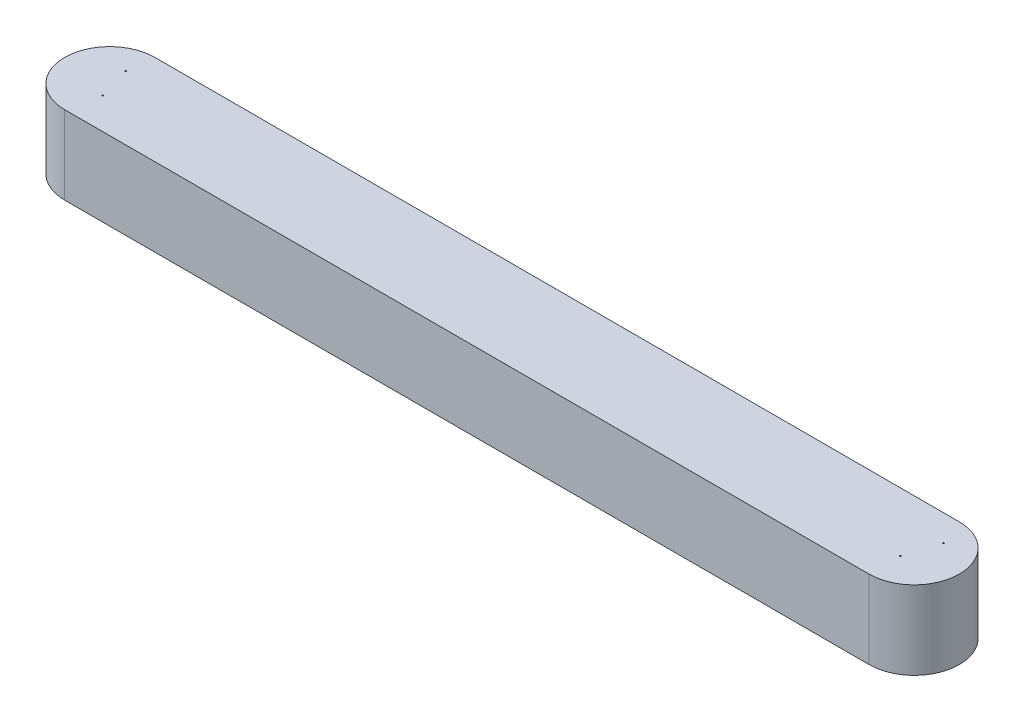
SolidWorks part; units mm, degrees
ref_plane "Front Plane" through (0, 0, 0) normal (0, 0, 1) x (1, 0, 0)
ref_plane "Top Plane" through (0, 0, 0) normal (0, 1, 0) x (1, 0, 0)
ref_plane "Right Plane" through (0, 0, 0) normal (1, 0, 0) x (0, 0, -1)
sketch "Sketch1" plane through (0, 0, 0) normal (0, 1, 0) x (1, 0, 0)
  line L0 (0, 0) -> (-763.029, 0) construction
  line L1 (0, -42.854) -> (-763.029, -42.854)
  line L2 (0, 42.854) -> (-763.029, 42.854)
  arc A0 (0, -42.854) -> (0, 42.854) centre (0, 0) ccw
  arc A1 (-763.029, 42.854) -> (-763.029, -42.854) centre (-763.029, 0) ccw
  point P3 (-381.5145, 0)
  dimension "D2" = 42.854
  dimension "D1" = 763.029
extrude "Boss-Extrude1" add sketch "Sketch1" along normal blind 74.3411
hole_wizard "#0-80 Tapped Hole2" positions "Sketch4" profile "Sketch5" tap size "#0-80" standard "ANSI Inch" end condition through all
sketch "Sketch4" plane through (0, 74.3411, 0) normal (0, 1, 0) x (1, 0, 0)
  point P0 (9.863, 17.8798)
  point P2 (0, -13.0738)
  point P4 (-765.8535, 17.8798)
  point P6 (-756.4736, -13.0738)
sketch "Sketch5" plane through (9.863, 74.3411, -17.8798) normal (1, 0, 0) x (0, 0, 1)
  line L0 (0, 0) -> (0, 74.3411)
  line L1 (0, 74.3411) -> (0.5956, 74.3411)
  line L2 (0.5956, 74.3411) -> (0.5956, 0)
  line L5 (0.5956, 0) -> (0, 0)
  line L11 (0, -6.35) -> (0, 107.95) construction
  dimension "Thru Tap Drill Dia." = 1.1913
  dimension "Thru Tap Drill Depth" = 74.3411
cosmetic thread "Hole Thread5" parameters "D2"=1.524
cosmetic thread "Hole Thread6" parameters "D2"=1.524
cosmetic thread "Hole Thread7" parameters "D2"=1.524
cosmetic thread "Hole Thread8" parameters "D2"=1.524
hole_wizard "#0-80 Tapped Hole1" positions "Sketch2" profile "Sketch3" tap size "#0-80" standard "ANSI Inch"
sketch "Sketch2" plane through (0, 74.3411, 0) normal (0, 1, 0) x (1, 0, 0)
  point P0 (0, 0)
  point P3 (-30.3793, -17.7803)
  point P5 (-514.8481, 0)
  point P7 (-494.9112, -17.7803)
sketch "Sketch3" plane through (0, 74.3411, 0) normal (1, 0, 0) x (0, 0, 1)
  line L0 (0, 0) -> (0, 74.3411)
  line L1 (0, 74.3411) -> (0.5956, 74.3411)
  line L2 (0.5956, 74.3411) -> (0.5956, 0)
  line L5 (0.5956, 0) -> (0, 0)
  line L11 (0, -6.35) -> (0, 107.95) construction
  dimension "Thru Tap Drill Dia." = 1.1913
  dimension "Thru Tap Drill Depth" = 74.3411
cosmetic thread "Hole Thread1" parameters "D2"=1.524
cosmetic thread "Hole Thread2" parameters "D2"=1.524
cosmetic thread "Hole Thread3" parameters "D2"=1.524
cosmetic thread "Hole Thread4" parameters "D2"=1.524
